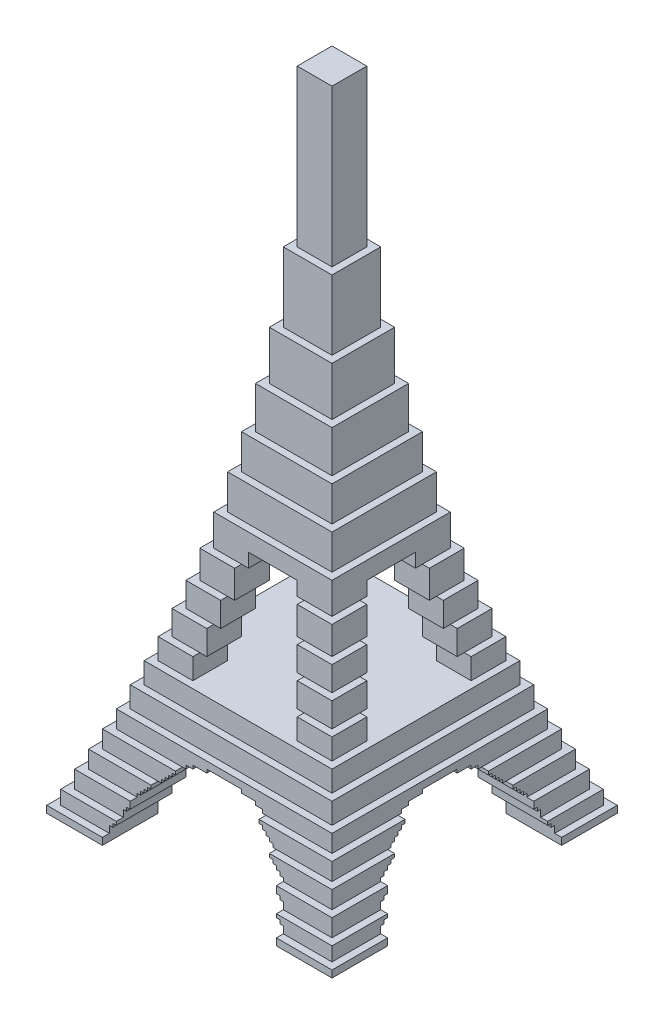
SolidWorks part; units mm, degrees
ref_plane "Ebene vorne" through (0, 0, 0) normal (0, 0, 1) x (1, 0, 0)
ref_plane "Ebene oben" through (0, 0, 0) normal (0, 1, 0) x (1, 0, 0)
ref_plane "Ebene rechts" through (0, 0, 0) normal (1, 0, 0) x (0, 0, -1)
sketch "Skizze1" plane through (0, 0, 0) normal (0, 0, 1) x (1, 0, 0)
  line L0 (0, 108) -> (0, 0) construction
  line L1 (-12.5, 0) -> (12.5, 0) construction
  line L2 (-12.5, 0) -> (-20.5, 0)
  line L3 (12.5, 0) -> (20.5, 0)
  line L4 (-2, 93) -> (2, 93)
  line L5 (-13.0623, 19) -> (13.0623, 19)
  line L6 (-7.8559, 38) -> (7.8559, 38)
  arc A0 (-2, 93) -> (2, 93) centre (0, 93) cw
  spline S0 degree 2 poles (-2, 93) (-2.3606, 39.4593) (-20.5, 0) knots 0 0 0 1 1 1
  spline S1 degree 2 poles (2, 93) (2.3606, 39.4593) (20.5, 0) knots 0 0 0 1 1 1
  spline S2 degree 2 poles (0, 93) (0.0715, 39.2735) (-12.5, 0) knots 0 0 0 1 1 1
  point P5 (0, 93)
  dimension "D5" = 19
  dimension "D1" = 108
  dimension "D2" = 41
  dimension "D3" = 25
  dimension "D4" = 15
  dimension "D6" = 38
  dimension "D7" = 4
sketch "Skizze3" plane through (0, 0, 0) normal (0, 1, 0) x (1, 0, 0)
  line L0 (0, -12.5) -> (0, 12.5) construction
  line L1 (-12.5, 0) -> (12.5, 0) construction
  line L2 (0, -12.5) -> (0, -20.5)
  line L3 (0, 12.5) -> (0, 20.5)
  line L4 (12.5, 0) -> (20.5, 0) construction
sketch "Skizze4" plane through (0, 0, 0) normal (0, 0, 1) x (1, 0, 0)
  line L1 (-20.5, 108) -> (20.5, 108)
  line L2 (-20.5, 108) -> (-20.5, 0)
  line L3 (-20.5, 0) -> (20.5, 0)
  line L4 (20.5, 108) -> (20.5, 0)
extrude "Aufsatz-Linear austragen2" add sketch "Skizze4" along normal up to vertex (20.5 mm away) and the other way up to vertex (20.5 mm away) up to point (0, 0, 20.5) other way up to point (0, 0, -20.5)
ref_plane "Ebene1" through (0, 0, 0) normal (0.7071, 0, 0.7071) x (0.7071, 0, -0.7071)
sketch "Skizze2" plane through (0, 0, 0) normal (0, 0, 1) x (1, 0, 0)
  line L1 (-12.5, 0) -> (-12.5, 2)
  line L4 (-2.5, 12) -> (0, 12)
  line L5 (0, 108) -> (0, 0) construction
  line L6 (-2.5, 12) -> (-2.5, 11.5)
  line L7 (-2.5, 11.5) -> (-4.5, 11.5)
  line L8 (-4.5, 11.5) -> (-4.5, 11)
  line L9 (-4.5, 11) -> (-5.5, 11)
  line L10 (-5.5, 11) -> (-5.5, 10.5)
  line L11 (-5.5, 10.5) -> (-6, 10.5)
  line L12 (-6, 10.5) -> (-6, 10)
  line L13 (-6, 10) -> (-6.5, 10)
  line L14 (-6.5, 10) -> (-6.5, 9.5)
  line L15 (-6.5, 9.5) -> (-7, 9.5)
  line L16 (-7, 9.5) -> (-7, 9)
  line L17 (-7, 9) -> (-7.5, 9)
  line L18 (-7.5, 9) -> (-7.5, 8.5)
  line L19 (-7.5, 8.5) -> (-8, 8.5)
  line L20 (-8, 8.5) -> (-8, 8)
  line L21 (-8, 8) -> (-8.5, 8)
  line L22 (-8.5, 8) -> (-8.5, 7.5)
  line L23 (-8.5, 7.5) -> (-9, 7.5)
  line L24 (-9, 7.5) -> (-9, 7)
  line L26 (-9, 7) -> (-9.5, 7)
  line L27 (-13.0623, 19) -> (13.0623, 19) construction
  line L28 (-9.5, 7) -> (-9.5, 6.5)
  line L29 (-9.5, 6.5) -> (-10, 6.5)
  line L30 (-10, 6.5) -> (-10, 6)
  line L31 (-10, 6) -> (-10.5, 6)
  line L32 (-10.5, 6) -> (-10.5, 4.5)
  line L33 (-10.5, 4.5) -> (-11, 4.5)
  line L34 (-11, 4.5) -> (-11, 4)
  line L35 (-11, 4) -> (-11.5, 4)
  line L36 (-11.5, 4) -> (-11.5, 2.5)
  line L37 (-11.5, 2.5) -> (-12, 2.5)
  line L38 (-12, 2.5) -> (-12, 2)
  line L39 (-12, 2) -> (-12.5, 2)
  line L59 (0, 12) -> (0, 0)
  line L60 (0, 0) -> (-12.5, 0)
  dimension "D1" = 2.5
  dimension "D2" = 2
  dimension "D3" = 1
  dimension "D4" = 0.5
  dimension "D5" = 7
  dimension "D6" = 4
  dimension "D7" = 0.5
  dimension "D8" = 1.5
  dimension "D9" = 1.5
  dimension "D10" = 2
extrude "Schnitt-Linear austragen1" cut sketch "Skizze2" against normal through all and the other way through all
sketch "Skizze5" plane through (0, 0, 0) normal (0, 0, 1) x (1, 0, 0)
  line L0 (-20.5, 0) -> (-30.5, 0)
  line L1 (-20.5, 108) -> (-20.5, 0) construction
  line L2 (-14.5, 16) -> (-13.5, 16)
  line L3 (-13.5, 16) -> (-13.5, 19)
  line L4 (-8.5, 37.5) -> (-7.5, 37.5)
  line L5 (-7.5, 37.5) -> (-7.5, 42.5)
  line L6 (-7.5, 42.5) -> (-6.5, 42.5)
  line L7 (-6.5, 42.5) -> (-6.5, 47.5)
  line L8 (-6.5, 47.5) -> (-5.5, 47.5)
  line L9 (-5.5, 47.5) -> (-5.5, 53.5)
  line L10 (-5.5, 53.5) -> (-4.5, 53.5)
  line L11 (-4.5, 53.5) -> (-4.5, 60.5)
  line L12 (-4.5, 60.5) -> (-3.5, 60.5)
  line L13 (-3.5, 60.5) -> (-3.5, 70.5)
  line L14 (-3.5, 70.5) -> (-2.5, 70.5)
  line L16 (20.5, 108) -> (-20.5, 108) construction
  line L17 (-2.5, 70.5) -> (-2.5, 93)
  line L18 (-2.5, 93) -> (0, 93)
  line L25 (-13.5, 19) -> (-12.5, 19)
  line L42 (-20.5, 0) -> (-20.5, 1)
  line L43 (-20.5, 1) -> (-19.5, 1)
  line L44 (-19.5, 1) -> (-19.5, 3)
  line L45 (-19.5, 3) -> (-18.5, 3)
  line L46 (-18.5, 3) -> (-18.5, 5.5)
  line L47 (-18.5, 5.5) -> (-17.5, 5.5)
  line L48 (-17.5, 5.5) -> (-17.5, 8)
  line L49 (-17.5, 8) -> (-16.5, 8)
  line L50 (-16.5, 8) -> (-16.5, 10.5)
  line L51 (-16.5, 10.5) -> (-15.5, 10.5)
  line L52 (-15.5, 10.5) -> (-15.5, 13)
  line L53 (-15.5, 13) -> (-14.5, 13)
  line L54 (-14.5, 16) -> (-14.5, 13)
  line L56 (-30.5, 0) -> (-30.5, 118)
  line L57 (-30.5, 118) -> (0, 118)
  line L61 (-12.5, 19) -> (-12.5, 22)
  line L62 (-12.5, 22) -> (-11.5, 22)
  line L63 (-11.5, 22) -> (-11.5, 25.5)
  line L64 (-11.5, 25.5) -> (-10.5, 25.5)
  line L65 (-10.5, 25.5) -> (-10.5, 29)
  line L66 (-10.5, 29) -> (-9.5, 29)
  line L67 (-9.5, 29) -> (-9.5, 33)
  line L68 (-9.5, 33) -> (-8.5, 33)
  line L69 (-8.5, 33) -> (-8.5, 37.5)
  line L71 (0, 93) -> (0, 118)
  dimension "D2" = 4.5
  dimension "D3" = 2.5
  dimension "D4" = 3
  dimension "D5" = 3
  dimension "D6" = 3
  dimension "D7" = 3.5
  dimension "D8" = 3.5
  dimension "D9" = 4
  dimension "D10" = 2.5
  dimension "D11" = 5
  dimension "D12" = 5
  dimension "D13" = 1
  dimension "D14" = 1
  dimension "D15" = 6
  dimension "D16" = 10
  dimension "D17" = 2.5
  dimension "D18" = 7
  dimension "D19" = 10
  dimension "D20" = 2.5
  dimension "D21" = 2
  dimension "D22" = 10
extrude "Schnitt-Linear austragen2" cut sketch "Skizze5" against normal through all and the other way through all
sketch "Skizze6" plane through (0, 0, 0) normal (0, 0, 1) x (1, 0, 0)
  line L0 (0, 19) -> (-7.5, 19)
  line L1 (0, 108) -> (0, 0) construction
  line L2 (-7.5, 19) -> (-7.5, 22)
  line L3 (-7.5, 22) -> (-6.5, 22)
  line L4 (-6.5, 22) -> (-6.5, 25.5)
  line L5 (-6.5, 25.5) -> (-5.5, 25.5)
  line L6 (-5.5, 25.5) -> (-5.5, 29)
  line L7 (-5.5, 29) -> (-4.5, 29)
  line L8 (-12.5, 0) -> (12.5, 0) construction
  line L9 (-4.5, 33) -> (-3.5, 33)
  line L10 (-4.5, 33) -> (-4.5, 29)
  line L11 (-3.5, 33) -> (-3.5, 35)
  line L12 (0, 35) -> (0, 19)
  line L13 (-3.5, 35) -> (0, 35)
  line L16 (-13.0623, 19) -> (13.0623, 19) construction
  dimension "D1" = 7.5
  dimension "D2" = 3
  dimension "D3" = 1
  dimension "D4" = 3.5
  dimension "D5" = 3.5
  dimension "D6" = 35
  dimension "D7" = 4
  dimension "D8" = 3.5
extrude "Schnitt-Linear austragen5" cut sketch "Skizze6" against normal through all and the other way through all
mirror "Spiegeln2" about plane through (0, 0, 0) normal (1, 0, 0) of "Schnitt-Linear austragen5", "Schnitt-Linear austragen1", "Schnitt-Linear austragen2"
mirror "Spiegeln1" about plane through (0, 0, 0) normal (0.7071, 0, 0.7071) of "Schnitt-Linear austragen5", "Spiegeln2", "Schnitt-Linear austragen1", "Schnitt-Linear austragen2"
